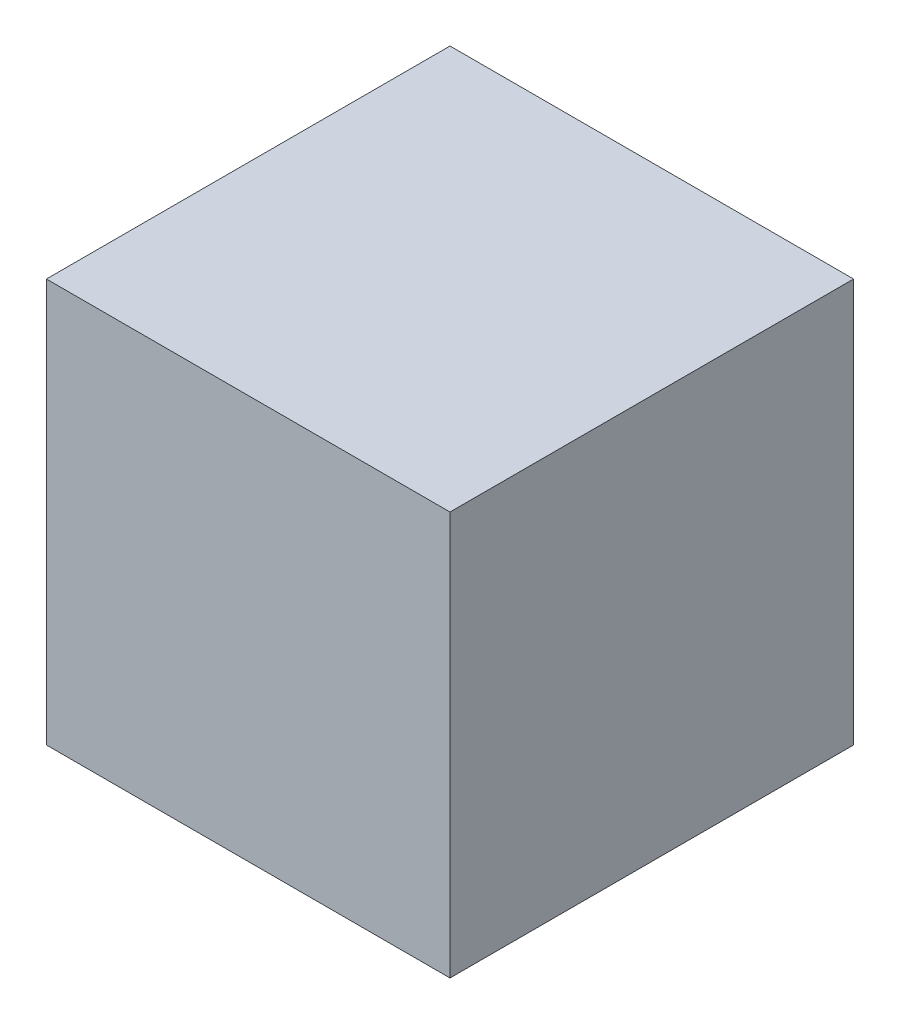
SolidWorks part; units mm, degrees
ref_plane "正面" through (0, 0, 0) normal (0, 0, 1) x (1, 0, 0)
ref_plane "平面" through (0, 0, 0) normal (0, 1, 0) x (1, 0, 0)
ref_plane "右側面" through (0, 0, 0) normal (1, 0, 0) x (0, 0, -1)
sketch "ｽｹｯﾁ1" plane through (0, 0, 0) normal (0, 0, 1) x (1, 0, 0)
  line L1 (0, 0) -> (700, 0)
  line L2 (0, 0) -> (0, 700)
  line L3 (0, 700) -> (700, 700)
  line L4 (700, 0) -> (700, 700)
  dimension "D1" = 700
  dimension "D2" = 700
extrude "ﾎﾞｽ - 押し出し1" add sketch "ｽｹｯﾁ1" along normal blind 700
